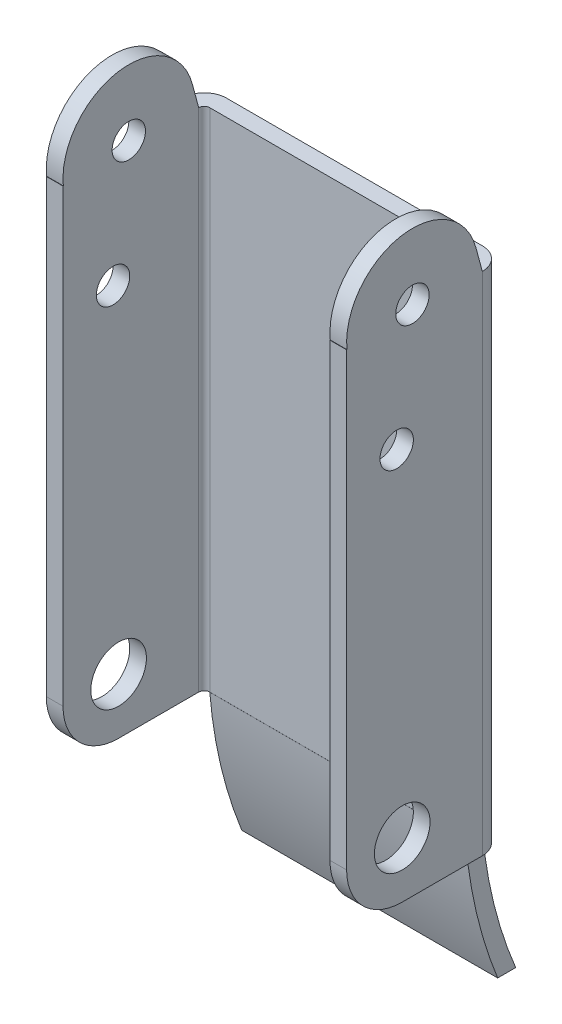
SolidWorks part; units mm, degrees
material "AISI 304"
ref_plane "Front" through (0, 0, 0) normal (0, 0, 1) x (1, 0, 0)
ref_plane "Top" through (0, 0, 0) normal (0, 1, 0) x (1, 0, 0)
ref_plane "Right" through (0, 0, 0) normal (1, 0, 0) x (0, 0, -1)
sketch "Sketch1" plane through (0, 0, 0) normal (0, 1, 0) x (1, 0, 0)
  line L0 (0, 0) -> (0, 36.2133) construction
  line L1 (13.5, 0) -> (13.5, 12.2)
  line L2 (-13.5, 0) -> (-13.5, 12.2)
  line L3 (-12, 0) -> (-13.5, 0)
  line L4 (11.5, 14.2) -> (-11.5, 14.2)
  line L5 (0, 14.2) -> (-22.6224, 14.2) construction
  line L6 (13.5, 0) -> (13.5, 36.2133) construction
  line L7 (-13.5, 0) -> (-13.5, 36.2133) construction
  line L8 (-12, 0) -> (-12, 12.2)
  line L9 (11.5, 12.7) -> (-11.5, 12.7)
  line L10 (12, 0) -> (12, 12.2)
  line L11 (12, 0) -> (13.5, 0)
  line L12 (0, 0) -> (-22.6224, 0) construction
  arc A0 (13.5, 12.2) -> (11.5, 14.2) centre (11.5, 12.2) ccw
  arc A1 (-11.5, 14.2) -> (-13.5, 12.2) centre (-11.5, 12.2) ccw
  arc A2 (-11.5, 12.7) -> (-12, 12.2) centre (-11.5, 12.2) ccw
  arc A3 (12, 12.2) -> (11.5, 12.7) centre (11.5, 12.2) ccw
  dimension "D4" = 2
  dimension "D1" = 13.5
  dimension "D2" = 13.5
  dimension "D3" = 14.2
  dimension "D5" = 1.5
extrude "Boss-Extrude1" add sketch "Sketch1" along normal blind 52
sketch "Sketch2" plane through (0, 0, 0) normal (1, 0, 0) x (0, 0, -1)
  line L1 (12.2, 52) -> (12.2, 0) construction
  line L2 (12.2, 52) -> (12.2, 0) construction
  line L4 (12.2, 45.5) -> (11.6336, 47.614)
  line L5 (0, 45.5) -> (12.2, 45.5)
  line L6 (-2.3308, 45.5) -> (0.0287, 45.5)
  line L7 (16.336, 45.5) -> (16.336, 58.0464)
  line L8 (16.336, 58.0464) -> (-2.3308, 58.0464)
  line L9 (-2.3308, 58.0464) -> (-2.3308, 45.5)
  line L10 (12.2, 45.5) -> (16.336, 45.5)
  line L11 (0, 52) -> (0, 0) construction
  line L12 (12.2, 0) -> (0, 0) construction
  line L13 (0, 5) -> (0, 0)
  line L14 (5, 0) -> (0, 0)
  line L17 (0, 35.5) -> (12.2, 35.5)
  line L18 (4.5, 35.5) -> (12.2, 35.5) construction
  line L20 (4.5, 52) -> (4.5, 0)
  line L21 (4.5, 52) -> (4.5, 35.5) construction
  arc A0 (11.6336, 47.614) -> (0.0287, 45.5) centre (5.9176, 46.0824) ccw
  arc A1 (5, 0) -> (0, 5) centre (5, 5) cw
  circle A2 centre (5, 5) radius 2.5
  circle A3 centre (5.9176, 46.0824) radius 1.5
  circle A4 centre (4.5, 35.5) radius 1.5
  dimension "D3" = 5
  dimension "D4" = 5
  dimension "D5" = 3
  dimension "D8" = 3
  dimension "D2" = 15
  dimension "D1" = 6.5
  dimension "D6" = 16.5
  dimension "D7" = 4.5
extrude "Cut-Extrude1" cut sketch "Sketch2" against normal mid plane 52
sketch "Sketch4" plane through (0, 0, 0) normal (1, 0, 0) x (0, 0, -1)
  line L0 (5.9176, 52) -> (25.1228, 52) construction
  line L4 (14.2, 45.5) -> (14.2, 0) construction
  line L5 (14.2, 45.5) -> (14.2, 0) construction
  line L6 (5, -12.2) -> (12.2, -12.2)
  line L7 (5, -12.2) -> (17.2, -12.2) construction
  line L8 (12.7, 45.5) -> (12.7, 0) construction
  line L9 (12.7, 45.5) -> (12.7, 0) construction
  line L10 (12.2, 0) -> (14.2, 0) construction
  line L11 (12.6946, 0) -> (14.2, 0)
  line L12 (15.579, -12.2) -> (17.2, -12.2)
  arc A0 (11.6336, 47.614) -> (0.0287, 45.5) centre (5.9176, 46.0824) ccw construction
  arc A1 (14.2, 0) -> (17.2, -12.2) centre (54.6875, 3.4871) ccw
  arc A2 (12.6946, 0) -> (15.579, -12.2) centre (54.6875, 3.4871) ccw
  arc A3 (12.7055, -0.1287) -> (15.8163, -12.779) centre (54.6875, 3.4871) ccw construction
  arc A4 (14.2, 0) -> (17.2, -12.2) centre (54.6875, 3.4871) ccw construction
  dimension "D1" = 1.5
  dimension "D2" = 12.2
extrude "Boss-Extrude2" add sketch "Sketch4" along normal up to vertex (11.5 mm away) and the other way up to vertex (11.5 mm away)
